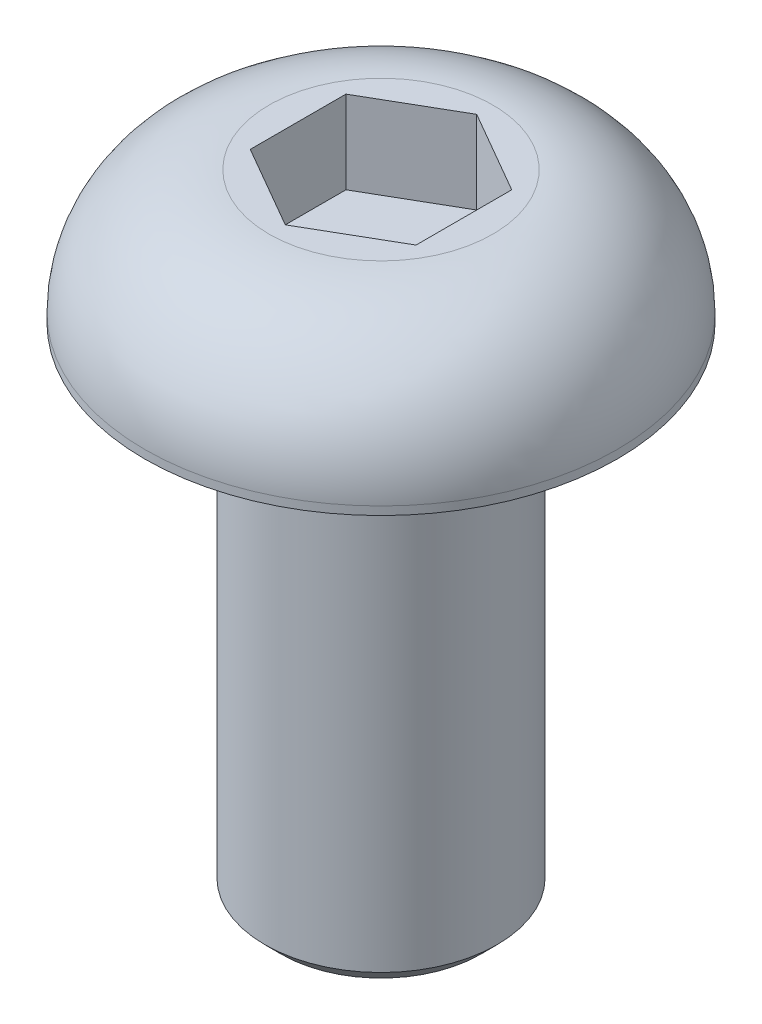
SolidWorks part; units mm, degrees
material "铸造合金钢"
ref_plane "前视基准面" through (0, 0, 0) normal (0, 0, 1) x (1, 0, 0)
ref_plane "上视基准面" through (0, 0, 0) normal (0, 1, 0) x (1, 0, 0)
ref_plane "右视基准面" through (0, 0, 0) normal (1, 0, 0) x (0, 0, -1)
sketch "草图1" plane through (0, 0, 0) normal (0, 1, 0) x (1, 0, 0)
  circle A0 centre (0, 0) radius 2.85
  dimension "D1" = 5.7
extrude "凸台-拉伸1" add sketch "草图1" along normal blind 1.6
sketch "草图2" plane through (0, 1.6, 0) normal (0, 1, 0) x (1, 0, 0)
  line L1 (0, -1.1547) -> (1, -0.5774)
  line L2 (1, -0.5774) -> (1, 0.5774)
  line L3 (1, 0.5774) -> (0, 1.1547)
  line L4 (0, 1.1547) -> (-1, 0.5774)
  line L5 (-1, 0.5774) -> (-1, -0.5774)
  line L6 (-1, -0.5774) -> (0, -1.1547)
  circle A0 centre (0, 0) radius 1 construction
  dimension "D1" = 2
extrude "切除-拉伸1" cut sketch "草图2" against normal blind 1
fillet "圆角1" radius 1.5 1 edges at (0, 1.6, 2.85)
sketch "草图3" plane through (0, 0, 0) normal (0, -1, 0) x (1, 0, 0)
  circle A0 centre (0, 0) radius 1.4
  dimension "D1" = 2.8
extrude "凸台-拉伸2" add sketch "草图3" along normal blind 6
chamfer "倒角1" distance 0.2 angle 45 1 edges at (0, -6, -1.4)
